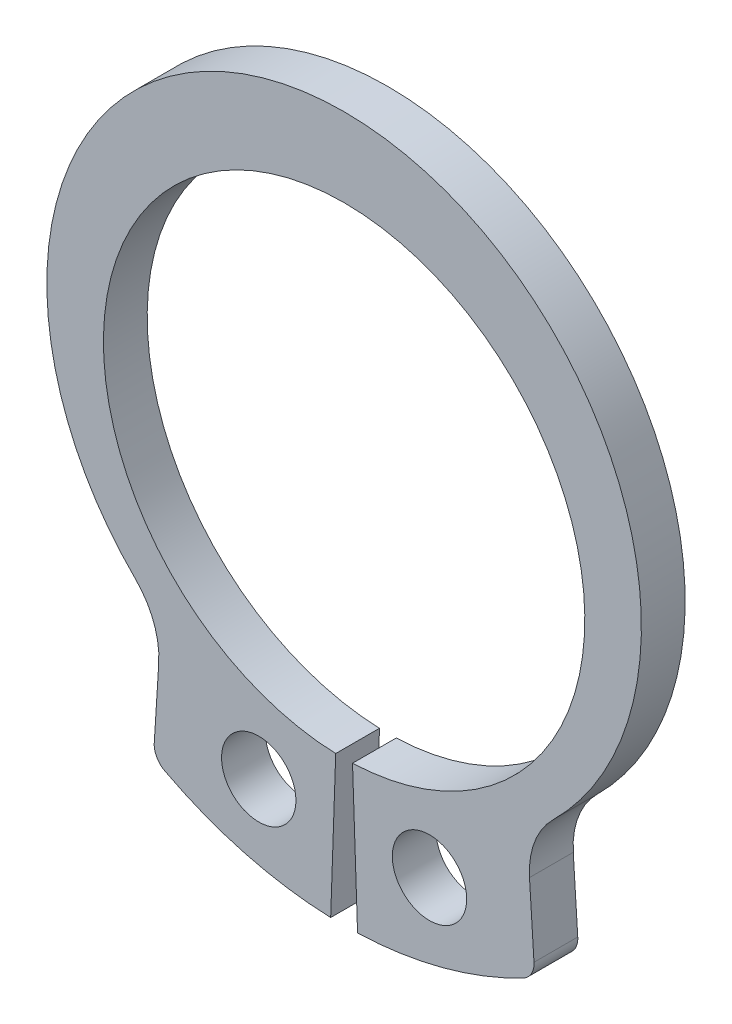
SolidWorks part; units mm, degrees
material "Plain Carbon Steel"
ref_plane "Front" through (0, 0, 0) normal (0, 0, 1) x (1, 0, 0)
ref_plane "Top" through (0, 0, 0) normal (0, 1, 0) x (1, 0, 0)
ref_plane "Right" through (0, 0, 0) normal (1, 0, 0) x (0, 0, -1)
sketch "Sketch1" plane through (0, 0, 0) normal (0, 0, 1) x (1, 0, 0)
  line L0 (0, 0) -> (-4.7631, -2.75) construction
  line L1 (0, 8.8) -> (0, -8.8) construction
  line L2 (-4.3566, -7.6521) -> (-4.1796, -4.8467) construction
  line L4 (-4.1796, -4.8467) -> (-4.7674, -5.5283) construction
  line L5 (-4.1796, -4.8467) -> (0, 0) construction
  line L6 (0, 5.5) -> (0, 7.3) construction
  line L7 (0, 7.3) -> (0, 6.4) construction
  line L8 (0, -5.5) -> (0, -8.8) construction
  line L9 (-2.4015, -8.4715) -> (0, 0) construction
  line L10 (0, 0) -> (-0.3073, -8.8) construction
  line L11 (-4.3566, -7.6521) -> (0, 0) construction
  line L12 (-4.2293, -5.6343) -> (-4.7724, -4.3258) construction
  line L13 (-4.5009, -4.98) -> (-4.1796, -4.8467) construction
  line L14 (-1.5001, -5.2915) -> (-2.4015, -8.4715) construction
  line L15 (-1.9508, -6.8815) -> (-1.133, -7.1133) construction
  arc A0 (0, 7.3) -> (-4.1796, -4.8467) centre (0, 0.5075) ccw construction
  circle A2 centre (0, 0) radius 7.3 construction
  arc A3 (-4.3566, -7.6521) -> (-0.3073, -8.8) centre (0, 0) ccw construction
  circle A4 centre (0, 0) radius 5.5 construction
  circle A6 centre (-1.9508, -6.8815) radius 0.85 construction
  arc A7 (-4.7724, -4.3258) -> (-4.2293, -5.6343) centre (-6.0556, -5.6254) cw construction
  point P5 (-4.7631, -2.75)
  point P24 (-3.6118, -6.3439)
  point P35 (0, 7.3)
  point P36 (0, 5.5)
  point P37 (0, -5.5)
  point P38 (0, -8.8)
  dimension "Ring ID" = 11
  dimension "Hole Diameter" = 1.7
  dimension "D10" = 1.8263
  dimension "Max Sec." = 1.8
  dimension "Lug Height" = 3.3
  dimension "D6" = 2
  dimension "D5" = 2.811
  dimension "D8" = 1.4167
  dimension "D3" = 120
  dimension "D2" = 4.25
  dimension "D4" = 1.4167
sketch "Sketch2" plane through (0, 0, 0) normal (0, 1, 0) x (1, 0, 0)
  line L0 (-7.3, 0.5) -> (-7.3, -0.5) construction
  line L2 (0, 0.5) -> (0, -0.5) construction
  line L4 (-7.3, 0) -> (7.3, 0) construction
  point P3 (-7.3, 0)
  point P6 (0, 0)
  dimension "Ring Thickness" = 1
sketch "Sketch4" plane through (0, 0, 0) normal (0, 0, 1) x (1, 0, 0)
  line L0 (-4.3566, -7.6521) -> (-4.1796, -4.8467) construction
  line L1 (-4.3566, -7.6521) -> (-4.1796, -4.8467)
  line L2 (0, 7.3) -> (0, 5.5)
  line L3 (-0.3073, -8.8) -> (-0.1919, -5.4966)
  line L4 (0, 0) -> (-0.3073, -8.8) construction
  arc A0 (0, 7.3) -> (-4.1796, -4.8467) centre (0, 0.5075) ccw construction
  arc A1 (-4.3566, -7.6521) -> (-0.3073, -8.8) centre (0, 0) ccw construction
  circle A2 centre (-1.9508, -6.8815) radius 0.85 construction
  arc A4 (0, 7.3) -> (-4.1796, -4.8467) centre (0, 0.5075) ccw
  arc A5 (-4.3566, -7.6521) -> (-0.3073, -8.8) centre (0, 0) ccw
  circle A6 centre (-1.9508, -6.8815) radius 0.85
  circle A7 centre (0, 0) radius 5.5 construction
  arc A8 (0, 5.5) -> (-0.1919, -5.4966) centre (0, 0) ccw
extrude "Boss-Extrude1" add sketch "Sketch4" along normal mid plane 1
fillet "Fillet1" radius 1.8263 1 edges at (-4.1796, -4.8467, 0)
fillet "Fillet2" radius 0.4566 1 edges at (-4.3566, -7.6521, 0)
mirror "Mirror1" about plane through (0, 7.3, 0.5) normal (-1, 0, 0) of bodies 109
sketch "Sketch3" plane through (0, 0, 0.5) normal (0, 0, 1) x (1, 0, 0)
  line L0 (4.1118, -3.6528) -> (4.7747, -4.3236) construction
  line L1 (4.7747, -4.3236) -> (5.4455, -3.6606) construction
  line L2 (0, 7.3) -> (0, 5.5) construction
  circle A0 centre (0, 0) radius 5.5 construction
  arc A1 (4.7747, -4.3236) -> (-4.7747, -4.3236) centre (0, 0.5075) ccw construction
equation "\"D1@Fillet1\" = \"D10@Sketch1\""
equation "\"D1@Fillet2\" = \"D10@Sketch1\" / 4"
equation "\"Thickness@Boss-Extrude1\"  = \"Ring Thickness@Sketch5\""
equation "\"D2@Sketch1\"=\"Hole Diameter@Sketch1\"*2.5"
equation "\"D4@Sketch1\"=\"D2@Sketch1\"/3"
equation "\"D8@Sketch1\"=\"D4@Sketch1\""
